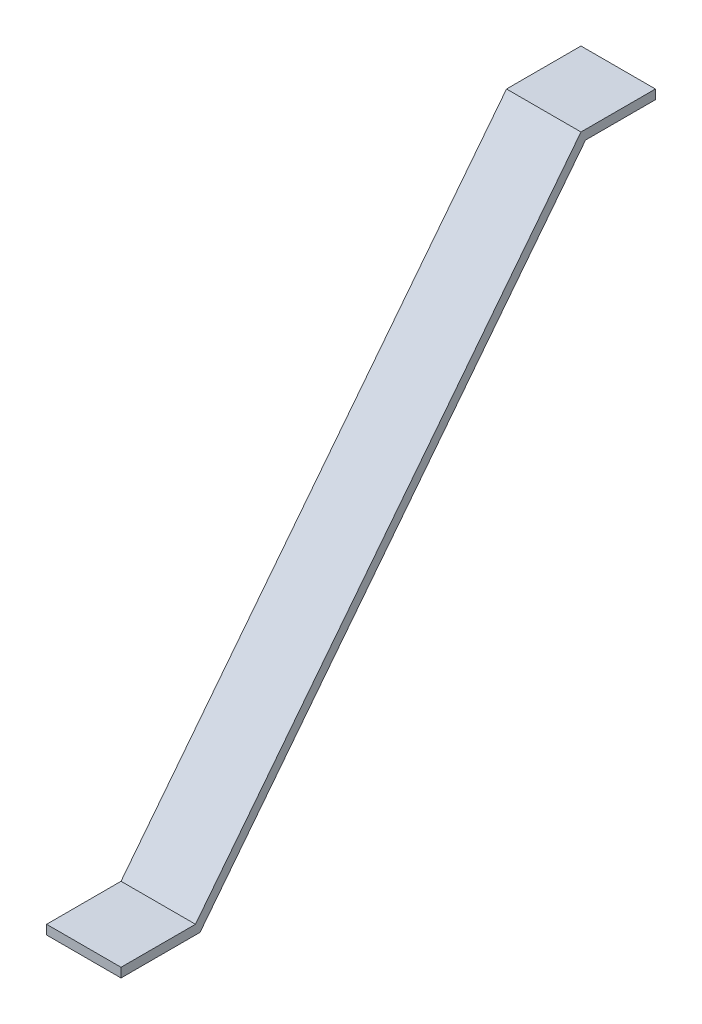
SolidWorks part; units mm, degrees
ref_plane "Front" through (0, 0, 0) normal (0, 0, 1) x (1, 0, 0)
ref_plane "Top" through (0, 0, 0) normal (0, 1, 0) x (1, 0, 0)
ref_plane "Right" through (0, 0, 0) normal (1, 0, 0) x (0, 0, -1)
sketch "Sketch1" plane through (0, 0, 0) normal (1, 0, 0) x (0, 0, -1)
  line L0 (-122.4566, -14.0399) -> (-97.0566, -14.0399)
  line L1 (-97.0566, -14.0399) -> (34.4487, 154.2792)
  line L2 (34.4487, 154.2792) -> (59.8487, 154.2792)
  line L3 (-122.4566, -17.2149) -> (-95.5081, -17.2149)
  line L4 (-95.5081, -17.2149) -> (35.9972, 151.1042)
  line L5 (35.9972, 151.1042) -> (59.8487, 151.1042)
  line L6 (-122.4566, -14.0399) -> (-122.4566, -17.2149)
  line L7 (59.8487, 154.2792) -> (59.8487, 151.1042)
  dimension "D1" = 213.6
  dimension "D2" = 25.4
  dimension "D3" = 25.4
  dimension "D5" = 128
  dimension "D4" = 3.175
extrude "Boss-Extrude1" add sketch "Sketch1" along normal blind 25.4
